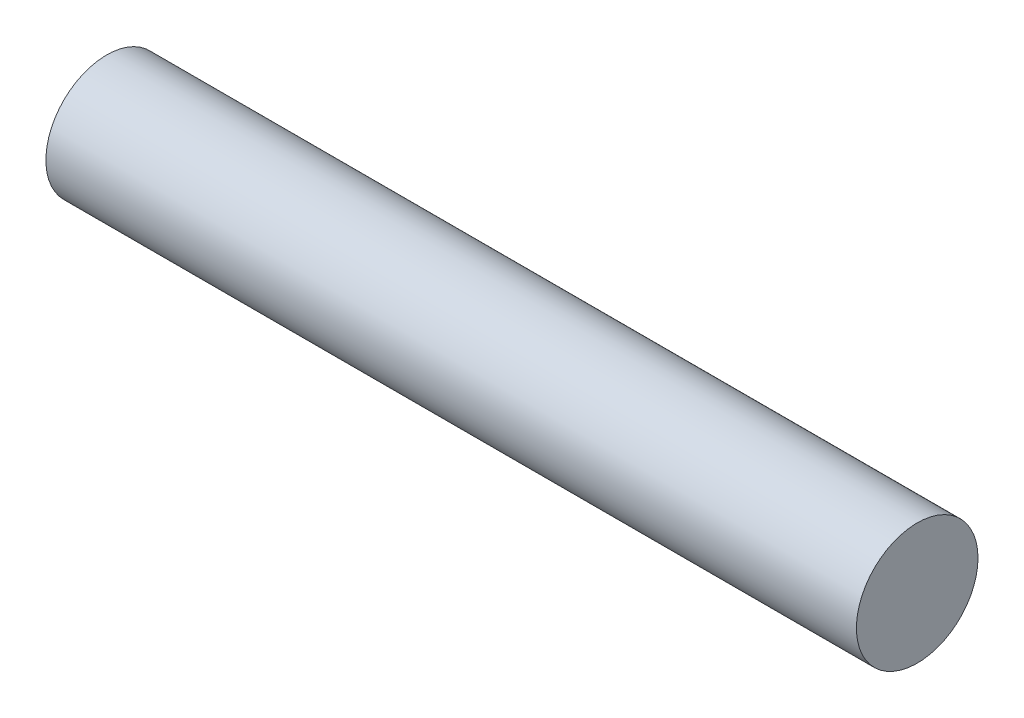
SolidWorks part; units mm, degrees
ref_plane "Front Plane" through (0, 0, 0) normal (0, 0, 1) x (1, 0, 0)
ref_plane "Top Plane" through (0, 0, 0) normal (0, 1, 0) x (1, 0, 0)
ref_plane "Right Plane" through (0, 0, 0) normal (1, 0, 0) x (0, 0, -1)
sketch "Sketch1" plane through (0, 0, 0) normal (1, 0, 0) x (0, 0, -1)
  circle A0 centre (0, 0) radius 9.525
extrude "Boss-Extrude1" add sketch "Sketch1" along normal blind 127
sketch "Sketch2" plane through (127, 0, 0) normal (1, 0, 0) x (0, 0, -1)
  line L0 (0, 0) -> (-9.525, 0) construction
  line L1 (-9.525, 0) -> (9.525, 0) construction
  circle A0 centre (0, 0) radius 9.525
